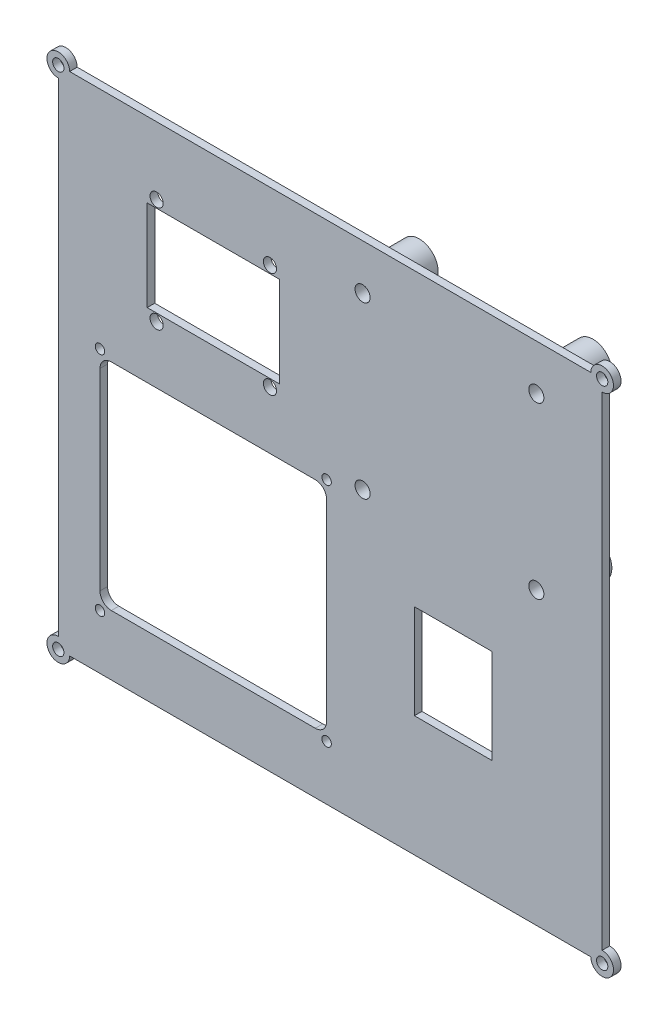
SolidWorks part; units mm, degrees
ref_plane "Front Plane" through (0, 0, 0) normal (0, 0, 1) x (1, 0, 0)
ref_plane "Top Plane" through (0, 0, 0) normal (0, 1, 0) x (1, 0, 0)
ref_plane "Right Plane" through (0, 0, 0) normal (1, 0, 0) x (0, 0, -1)
sketch "Sketch1" plane through (0, 0, 0) normal (0, 0, 1) x (1, 0, 0)
  line L4 (119.8009, -219.8036) -> (119.8009, -91.8036)
  line L5 (-21.1991, -222.8036) -> (116.8009, -222.8036)
  line L6 (-24.1991, -91.8036) -> (-24.1991, -219.8036)
  line L7 (116.8009, -88.8036) -> (-21.1991, -88.8036)
  arc A4 (119.8009, -91.8036) -> (116.8009, -88.8036) centre (119.8009, -88.8036) ccw
  arc A5 (116.8009, -222.8036) -> (119.8009, -219.8036) centre (119.8009, -222.8036) ccw
  arc A6 (-24.1991, -219.8036) -> (-21.1991, -222.8036) centre (-24.1991, -222.8036) ccw
  arc A7 (-21.1991, -88.8036) -> (-24.1991, -91.8036) centre (-24.1991, -88.8036) ccw
extrude "Boss-Extrude1" add sketch "Sketch1" along normal blind 2
sketch "Sketch2" plane through (0, 0, 0) normal (0, 0, -1) x (-1, 0, 0)
  circle A0 centre (-119.8009, -88.8036) radius 1.5
  circle A1 centre (24.1991, -88.8036) radius 1.5
  circle A2 centre (24.1991, -222.8036) radius 1.5
  circle A3 centre (-119.8009, -222.8036) radius 1.5
  dimension "D1" = 3
extrude "Cut-Extrude1" cut sketch "Sketch2" against normal blind 10
sketch "Sketch3" plane through (0, 0, 2) normal (0, 0, 1) x (1, 0, 0)
  line L1 (-13.1576, -148.3699) -> (46.8424, -148.3699) construction
  line L2 (-13.1576, -148.3699) -> (-13.1576, -208.3699) construction
  line L3 (-13.1576, -208.3699) -> (46.8424, -208.3699) construction
  line L4 (46.8424, -148.3699) -> (46.8424, -208.3699) construction
  circle A0 centre (-13.1576, -148.3699) radius 1.25
  circle A1 centre (46.8424, -148.3699) radius 1.25
  circle A2 centre (-13.1576, -208.3699) radius 1.25
  circle A3 centre (46.8424, -208.3699) radius 0.9585
  circle A4 centre (46.8424, -208.3699) radius 1.25
  dimension "D3" = 2.5
  dimension "D1" = 60
  dimension "D2" = 60
extrude "Cut-Extrude2" cut sketch "Sketch3" against normal blind 10
sketch "Sketch4" plane through (0, 0, 2) normal (0, 0, 1) x (1, 0, 0)
  line L0 (-13.1576, -208.3699) -> (46.8424, -148.3699) construction
  line L5 (-13.1576, -148.3699) -> (46.8424, -208.3699) construction
  line L7 (-10.1576, -149.8699) -> (43.8424, -149.8699)
  line L8 (-13.1576, -152.8699) -> (-13.1576, -203.8699)
  line L9 (-10.1576, -206.8699) -> (43.8424, -206.8699)
  line L10 (46.8424, -152.8699) -> (46.8424, -203.8699)
  line L11 (-13.1576, -149.8699) -> (46.8424, -206.8699) construction
  line L12 (-13.1576, -206.8699) -> (46.8424, -149.8699) construction
  arc A0 (43.8424, -206.8699) -> (46.8424, -203.8699) centre (43.8424, -203.8699) ccw
  arc A1 (-10.1576, -206.8699) -> (-13.1576, -203.8699) centre (-10.1576, -203.8699) cw
  arc A2 (46.8424, -152.8699) -> (43.8424, -149.8699) centre (43.8424, -152.8699) ccw
  arc A3 (-13.1576, -152.8699) -> (-10.1576, -149.8699) centre (-10.1576, -152.8699) cw
  point P4 (16.8424, -178.3699)
  dimension "D3" = 3
  dimension "D1" = 57
  dimension "D2" = 60
extrude "Cut-Extrude3" cut sketch "Sketch4" against normal blind 10
sketch "Sketch5" plane through (0, 0, 0) normal (0, 0, -1) x (-1, 0, 0)
  circle A2 centre (-46.8424, -208.3699) radius 0.9585
extrude "Cut-Extrude4" cut sketch "Sketch5" against normal blind 10
sketch "Sketch7" plane through (0, 0, 0) normal (0, 0, -1) x (-1, 0, 0)
  line L0 (-16.8424, -149.8699) -> (-16.8424, -97.9357) construction
  line L1 (-29.3424, -110.4098) -> (-4.3424, -110.4098)
  line L2 (-29.3424, -110.4098) -> (-29.3424, -130.9098)
  line L3 (-29.3424, -130.9098) -> (-4.3424, -130.9098)
  line L4 (-4.3424, -110.4098) -> (-4.3424, -130.9098)
  line L5 (-29.3424, -110.4098) -> (-4.3424, -130.9098) construction
  line L6 (-29.3424, -130.9098) -> (-4.3424, -110.4098) construction
  line L7 (-43.8424, -149.8699) -> (10.1576, -149.8699) construction
  point P0 (-16.8424, -120.6598)
  point P9 (-16.8424, -110.4098)
  dimension "D1" = 0
  dimension "D2" = 20.5
  dimension "D3" = 25
sketch "Sketch8" plane through (0, 0, 0) normal (0, 0, -1) x (-1, 0, 0)
  line L1 (-102.3691, -100.8849) -> (-56.3691, -100.8849) construction
  line L2 (-102.3691, -100.8849) -> (-102.3691, -145.8849) construction
  line L3 (-102.3691, -145.8849) -> (-56.3691, -145.8849) construction
  line L4 (-56.3691, -100.8849) -> (-56.3691, -145.8849) construction
  circle A0 centre (-102.3691, -100.8849) radius 2
  circle A1 centre (-56.3691, -100.8849) radius 2
  circle A2 centre (-102.3691, -145.8849) radius 2
  circle A3 centre (-56.3691, -145.8849) radius 2
  dimension "D3" = 4
  dimension "D1" = 45
  dimension "D2" = 46
extrude "Cut-Extrude7" cut sketch "Sketch8" against normal blind 10
sketch "Sketch9" plane through (0, 0, 2) normal (0, 0, 1) x (1, 0, 0)
  circle A0 centre (56.3691, -100.8849) radius 5
  circle A1 centre (56.3691, -100.8849) radius 2
  circle A2 centre (102.3691, -100.8849) radius 5
  circle A3 centre (102.3691, -100.8849) radius 2
  circle A4 centre (102.3691, -145.8849) radius 2
  circle A5 centre (102.3691, -145.8849) radius 5
  circle A6 centre (56.3691, -145.8849) radius 2
  circle A7 centre (56.3691, -145.8849) radius 5
  dimension "D1" = 10
extrude "Boss-Extrude2" add sketch "Sketch9" against normal blind 15
sketch "Sketch11" plane through (0, 0, 2) normal (0, 0, 1) x (1, 0, 0)
  line L0 (46.8424, -178.3699) -> (113.8394, -178.3699) construction
  line L1 (46.8424, -203.8699) -> (46.8424, -152.8699) construction
  line L3 (70.0909, -165.8699) -> (90.5909, -165.8699)
  line L4 (70.0909, -165.8699) -> (70.0909, -190.8699)
  line L5 (70.0909, -190.8699) -> (90.5909, -190.8699)
  line L6 (90.5909, -165.8699) -> (90.5909, -190.8699)
  line L7 (70.0909, -165.8699) -> (90.5909, -190.8699) construction
  line L8 (70.0909, -190.8699) -> (90.5909, -165.8699) construction
  point P4 (80.3409, -178.3699)
  dimension "D1" = 20.5
  dimension "D2" = 25
extrude "Cut-Extrude8" cut sketch "Sketch11" against normal blind 15
sketch "Sketch12" plane through (0, 0, 2) normal (0, 0, 1) x (1, 0, 0)
  line L0 (16.8424, -149.8699) -> (16.8424, -97.9357) construction
  line L2 (1.8424, -106.6598) -> (31.8424, -106.6598) construction
  line L3 (1.8424, -106.6598) -> (1.8424, -134.6598) construction
  line L4 (1.8424, -134.6598) -> (31.8424, -134.6598) construction
  line L5 (31.8424, -106.6598) -> (31.8424, -134.6598) construction
  line L6 (1.8424, -106.6598) -> (31.8424, -134.6598) construction
  line L7 (1.8424, -134.6598) -> (31.8424, -106.6598) construction
  line L8 (-0.6576, -108.6598) -> (34.3424, -108.6598)
  line L9 (-0.6576, -108.6598) -> (-0.6576, -132.6598)
  line L10 (-0.6576, -132.6598) -> (34.3424, -132.6598)
  line L11 (34.3424, -108.6598) -> (34.3424, -132.6598)
  line L12 (-0.6576, -108.6598) -> (34.3424, -132.6598) construction
  line L13 (-0.6576, -132.6598) -> (34.3424, -108.6598) construction
  circle A0 centre (31.8424, -106.6598) radius 1.75
  circle A1 centre (1.8424, -106.6598) radius 1.75
  circle A2 centre (1.8424, -134.6598) radius 1.75
  circle A3 centre (31.8424, -134.6598) radius 1.75
  point P4 (16.8424, -120.6598)
  point P14 (16.8424, -120.6598)
  dimension "D3" = 3.5
  dimension "D1" = 30
  dimension "D2" = 28
  dimension "D4" = 24
  dimension "D5" = 35
extrude "Cut-Extrude9" cut sketch "Sketch12" against normal blind 15
